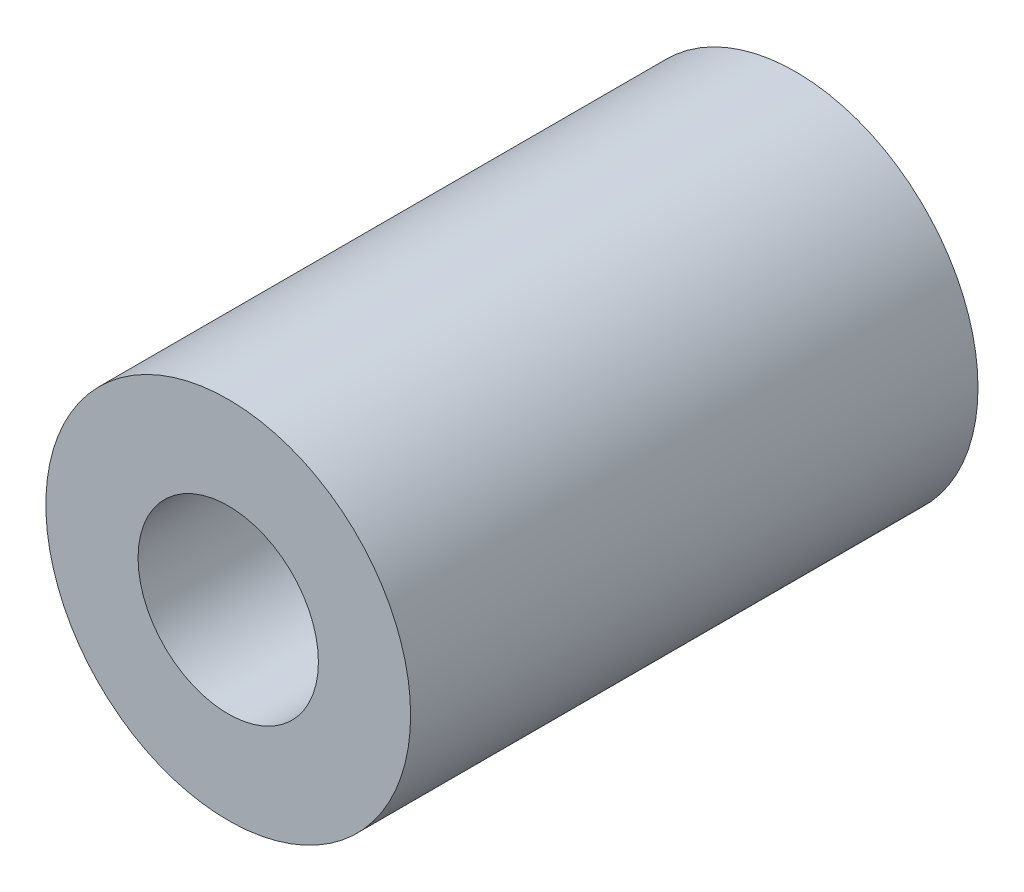
SolidWorks part; units mm, degrees
ref_plane "Front Plane" through (0, 0, 0) normal (0, 0, 1) x (1, 0, 0)
ref_plane "Top Plane" through (0, 0, 0) normal (0, 1, 0) x (1, 0, 0)
ref_plane "Right Plane" through (0, 0, 0) normal (1, 0, 0) x (0, 0, -1)
sketch "Sketch1" plane through (0, 0, 0) normal (0, 0, 1) x (1, 0, 0)
  circle A0 centre (0, 0) radius 5.1
  circle A1 centre (0, 0) radius 9
  dimension "D1" = 10.2
  dimension "D2" = 18
extrude "Boss-Extrude1" add sketch "Sketch1" along normal blind 16
sketch "Sketch2" plane through (0, 0, 16) normal (0, 0, 1) x (1, 0, 0)
  circle A0 centre (0, 0) radius 9 construction
  circle A1 centre (0, 0) radius 9
extrude "Boss-Extrude2" add sketch "Sketch2" along normal blind 12
sketch "Sketch5" plane through (0, 0, 28) normal (0, 0, 1) x (1, 0, 0)
  circle A0 centre (0, 0) radius 4.45
  dimension "D1" = 8.9
extrude "Cut-Extrude1" cut sketch "Sketch5" against normal blind 8
